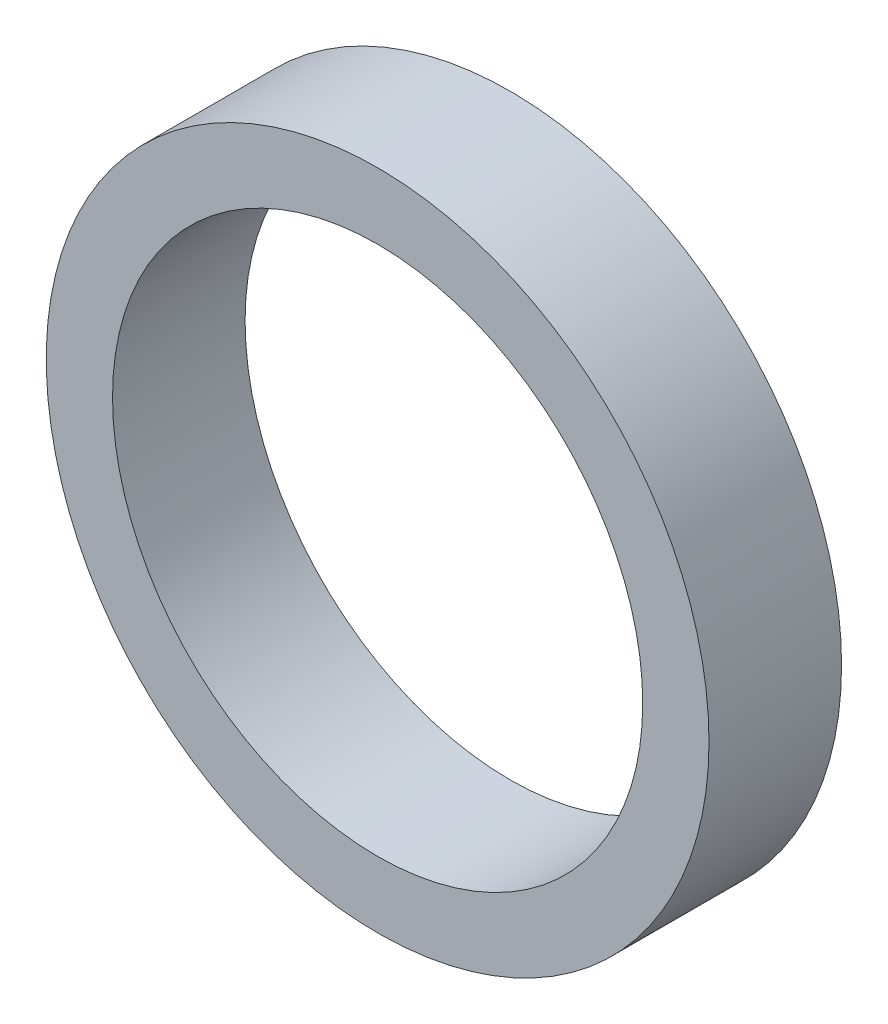
SolidWorks part; units mm, degrees
ref_plane "Front Plane" through (0, 0, 0) normal (0, 0, 1) x (1, 0, 0)
ref_plane "Top Plane" through (0, 0, 0) normal (0, 1, 0) x (1, 0, 0)
ref_plane "Right Plane" through (0, 0, 0) normal (1, 0, 0) x (0, 0, -1)
sketch "Sketch1" plane through (0, 0, 0) normal (0, 0, 1) x (1, 0, 0)
  circle A0 centre (0, 0) radius 4
  circle A1 centre (0, 0) radius 5
  dimension "D1" = 8
  dimension "D2" = 1
extrude "Boss-Extrude1" add sketch "Sketch1" along normal blind 2
